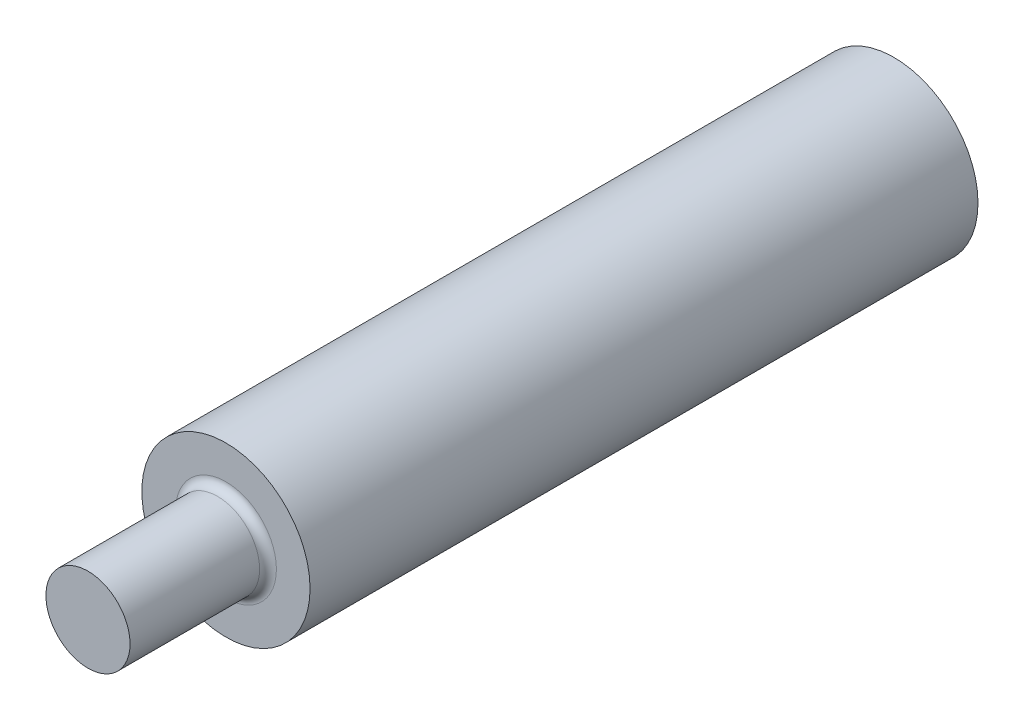
SolidWorks part; units mm, degrees
ref_plane "Front Plane" through (0, 0, 0) normal (0, 0, 1) x (1, 0, 0)
ref_plane "Top Plane" through (0, 0, 0) normal (0, 1, 0) x (1, 0, 0)
ref_plane "Right Plane" through (0, 0, 0) normal (1, 0, 0) x (0, 0, -1)
sketch "Sketch1" plane through (0, 0, 0) normal (0, 0, 1) x (1, 0, 0)
  circle A0 centre (0, 0) radius 25
  dimension "D1" = 50
extrude "Boss-Extrude1" add sketch "Sketch1" along normal blind 15
sketch "Sketch2" plane through (0, 0, 15) normal (0, 0, 1) x (1, 0, 0)
  circle A0 centre (0, 0) radius 50
  dimension "D1" = 100
extrude "Boss-Extrude2" add sketch "Sketch2" along normal blind 397
sketch "Sketch3" plane through (0, 0, 412) normal (0, 0, 1) x (1, 0, 0)
  circle A0 centre (0, 0) radius 25
  dimension "D1" = 50
extrude "Boss-Extrude3" add sketch "Sketch3" along normal blind 82
fillet "Fillet1" radius 5 2 edges at (25, 0, 412) (25, 0, 15)
ref_plane "Plane1" through (0, 0, 494) normal (0, 0, 1) x (1, 0, 0)
sketch "Sketch5" plane through (0, 0, 494) normal (0, 0, 1) x (1, 0, 0)
  line L0 (0, 27.6583) -> (0, 0) construction
  line L1 (-7.5, 27.6583) -> (7.5, 27.6583)
  line L2 (-7.5, 27.6583) -> (-7.5, 17.6583)
  line L3 (-7.5, 17.6583) -> (7.5, 17.6583)
  line L4 (7.5, 27.6583) -> (7.5, 17.6583)
  dimension "D1" = 10
  dimension "D2" = 15
